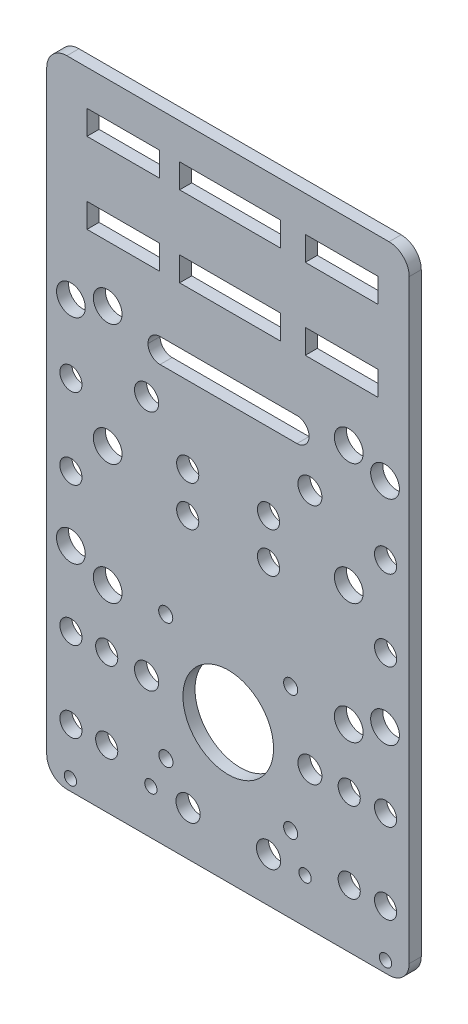
SolidWorks part; units mm, degrees
ref_plane "Front Plane" through (0, 0, 0) normal (0, 0, 1) x (1, 0, 0)
ref_plane "Top Plane" through (0, 0, 0) normal (0, 1, 0) x (1, 0, 0)
ref_plane "Right Plane" through (0, 0, 0) normal (1, 0, 0) x (0, 0, -1)
sketch "Model" plane through (0, 0, 0) normal (0, 0, 1) x (1, 0, 0)
  line L0 (-1583.9778, 1713.9264) -> (-1583.9778, 1719.9515)
  line L1 (-1583.9778, 1719.9515) -> (-1568.9758, 1719.9515)
  line L2 (-1568.9758, 1719.9515) -> (-1565.9758, 1719.9515)
  line L3 (-1565.9758, 1719.9515) -> (-1565.9758, 1713.9264)
  line L4 (-1565.9758, 1713.9264) -> (-1568.9758, 1713.9264)
  line L5 (-1568.9758, 1713.9264) -> (-1583.9778, 1713.9264)
  line L7 (-1638.1728, 1719.9515) -> (-1620.1708, 1719.9515)
  line L8 (-1638.1728, 1719.9515) -> (-1638.1728, 1713.9264)
  line L9 (-1638.1728, 1713.9264) -> (-1620.1708, 1713.9264)
  line L10 (-1620.1708, 1719.9515) -> (-1620.1708, 1713.9264)
  line L11 (-1638.1728, 1739.9515) -> (-1620.1708, 1739.9515)
  line L12 (-1583.9778, 1733.9264) -> (-1583.9778, 1739.9515)
  line L13 (-1583.9778, 1739.9515) -> (-1568.9758, 1739.9515)
  line L14 (-1568.9758, 1739.9515) -> (-1565.9758, 1739.9515)
  line L15 (-1565.9758, 1739.9515) -> (-1565.9758, 1733.9264)
  line L16 (-1565.9758, 1733.9264) -> (-1568.9758, 1733.9264)
  line L17 (-1568.9758, 1733.9264) -> (-1583.9778, 1733.9264)
  line L18 (-1638.1728, 1739.9515) -> (-1638.1728, 1733.9264)
  line L19 (-1638.1728, 1733.9264) -> (-1620.1708, 1733.9264)
  line L20 (-1620.1708, 1739.9515) -> (-1620.1708, 1733.9264)
  line L25 (-1590.1708, 1713.9264) -> (-1590.1708, 1719.9515)
  line L26 (-1590.1708, 1719.9515) -> (-1615.1728, 1719.9515)
  line L27 (-1615.1728, 1719.9515) -> (-1615.1728, 1713.9264)
  line L28 (-1615.1728, 1713.9264) -> (-1590.1708, 1713.9264)
  line L30 (-1590.1708, 1733.9264) -> (-1590.1708, 1739.9515)
  line L31 (-1590.1708, 1739.9515) -> (-1615.1728, 1739.9515)
  line L32 (-1615.1728, 1739.9515) -> (-1615.1728, 1733.9264)
  line L33 (-1615.1728, 1733.9264) -> (-1590.1708, 1733.9264)
  line L34 (-1558.1708, 1596.0316) -> (-1558.1708, 1743.759)
  line L35 (-1563.1708, 1748.7651) -> (-1643.1684, 1748.7651)
  line L36 (-1648.1684, 1743.759) -> (-1648.1684, 1596.0316)
  line L37 (-1643.1684, 1591.0316) -> (-1563.1708, 1591.0316)
  line L38 (-1583.0306, 1696.9558) -> (-1583.0306, 1696.9366)
  line L39 (-1586.0306, 1693.9366) -> (-1620.0306, 1693.9366)
  line L40 (-1623.0306, 1696.9366) -> (-1623.0306, 1696.9558)
  line L41 (-1620.0306, 1699.9558) -> (-1586.0306, 1699.9558)
  circle A0 centre (-1573.0631, 1605.4662) radius 2.75
  circle A1 centre (-1573.0631, 1625.4662) radius 2.75
  circle A2 centre (-1633.2761, 1605.4662) radius 2.75
  circle A3 centre (-1633.2761, 1625.4662) radius 2.75
  circle A4 centre (-1564.0347, 1605.4662) radius 2.75
  circle A5 centre (-1642.1661, 1605.4662) radius 2.75
  circle A6 centre (-1564.0347, 1625.4662) radius 2.75
  circle A7 centre (-1642.1661, 1625.4662) radius 2.75
  circle A8 centre (-1564.0521, 1593.8096) radius 1.524
  circle A9 centre (-1584.0288, 1602.0808) radius 1.524
  circle A10 centre (-1642.2871, 1593.8096) radius 1.524
  circle A11 centre (-1622.3104, 1602.0808) radius 1.524
  circle A12 centre (-1564.0347, 1679.893) radius 2.75
  circle A13 centre (-1564.0347, 1659.9362) radius 2.75
  circle A14 centre (-1642.1661, 1679.893) radius 2.75
  circle A15 centre (-1642.1661, 1659.9362) radius 2.75
  circle A16 centre (-1633.0289, 1669.9012) radius 3.57
  circle A17 centre (-1633.0276, 1699.992) radius 3.57
  circle A18 centre (-1633.0276, 1639.992) radius 3.57
  circle A19 centre (-1642.1684, 1643.8812) radius 3.57
  circle A20 centre (-1642.1684, 1696.8606) radius 3.57
  circle A21 centre (-1564.1708, 1643.8812) radius 3.57
  circle A22 centre (-1573.1719, 1669.9012) radius 3.57
  circle A23 centre (-1613.1661, 1674.8646) radius 2.75
  circle A24 centre (-1593.1004, 1674.8808) radius 2.75
  circle A25 centre (-1613.0771, 1602.0646) radius 3
  circle A26 centre (-1593.1004, 1602.0808) radius 3
  circle A27 centre (-1564.1708, 1696.8606) radius 3.57
  circle A28 centre (-1613.1661, 1664.8646) radius 2.75
  circle A29 centre (-1618.5721, 1609.9273) radius 1.75
  circle A30 centre (-1618.6255, 1640.9241) radius 1.75
  circle A31 centre (-1593.1004, 1664.8808) radius 2.75
  circle A32 centre (-1573.1732, 1699.992) radius 3.57
  circle A33 centre (-1623.3701, 1685.3605) radius 3
  circle A34 centre (-1582.8197, 1685.4661) radius 2.9887
  circle A35 centre (-1623.3701, 1625.3605) radius 3
  circle A36 centre (-1582.8197, 1625.4661) radius 2.9887
  circle A37 centre (-1587.6036, 1609.9524) radius 1.75
  circle A38 centre (-1587.6004, 1640.9492) radius 1.75
  circle A39 centre (-1603.1004, 1625.4524) radius 11.25
  circle A40 centre (-1573.1732, 1639.992) radius 3.57
  arc A41 (-1558.1708, 1743.759) -> (-1563.1708, 1748.7651) centre (-1563.1708, 1743.7651) ccw
  arc A42 (-1643.1684, 1748.7651) -> (-1648.1684, 1743.759) centre (-1643.1684, 1743.7651) ccw
  arc A43 (-1648.1684, 1596.0316) -> (-1643.1684, 1591.0316) centre (-1643.1684, 1596.0316) ccw
  arc A44 (-1563.1708, 1591.0316) -> (-1558.1708, 1596.0316) centre (-1563.1708, 1596.0316) ccw
  arc A45 (-1583.0306, 1696.9558) -> (-1586.0306, 1699.9558) centre (-1586.0306, 1696.9558) ccw
  arc A46 (-1586.0306, 1693.9366) -> (-1583.0306, 1696.9366) centre (-1586.0306, 1696.9366) ccw
  arc A47 (-1623.0306, 1696.9366) -> (-1620.0306, 1693.9366) centre (-1620.0306, 1696.9366) ccw
  arc A48 (-1620.0306, 1699.9558) -> (-1623.0306, 1696.9558) centre (-1620.0306, 1696.9558) ccw
extrude "Boss-Extrude2" add sketch "Model" along normal blind 3
